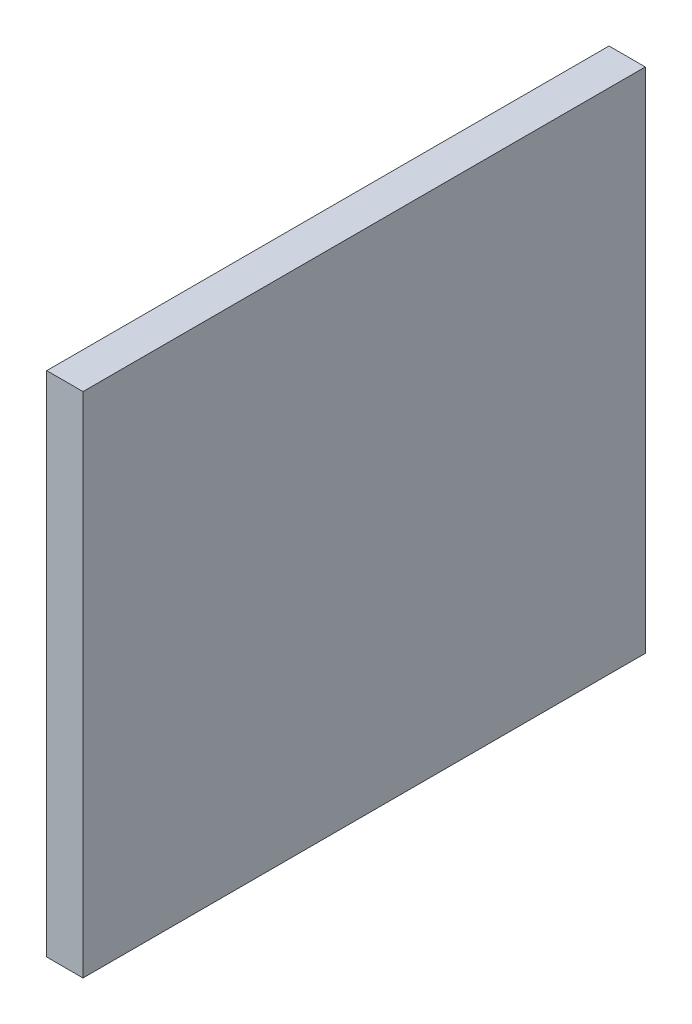
SolidWorks part; units mm, degrees
ref_plane "Front Plane" through (0, 0, 0) normal (0, 0, 1) x (1, 0, 0)
ref_plane "Top Plane" through (0, 0, 0) normal (0, 1, 0) x (1, 0, 0)
ref_plane "Right Plane" through (0, 0, 0) normal (1, 0, 0) x (0, 0, -1)
sketch "Sketch1" plane through (0, 0, 0) normal (0, 0, 1) x (1, 0, 0)
  line L0 (0, 0) -> (0, -150) construction
  line L1 (0, -150) -> (150, -150) construction
  line L2 (150, -150) -> (150, 0) construction
  line L3 (150, -140) -> (150, 0)
  line L4 (150, 0) -> (160, 0)
  line L5 (160, 0) -> (160, -140)
  line L7 (150, -140) -> (160, -140)
  circle A0 centre (0, 0) radius 150 construction
  dimension "D1" = 300
  dimension "D2" = 10
  dimension "D3" = 10
extrude "Boss-Extrude1" add sketch "Sketch1" along normal blind 155
